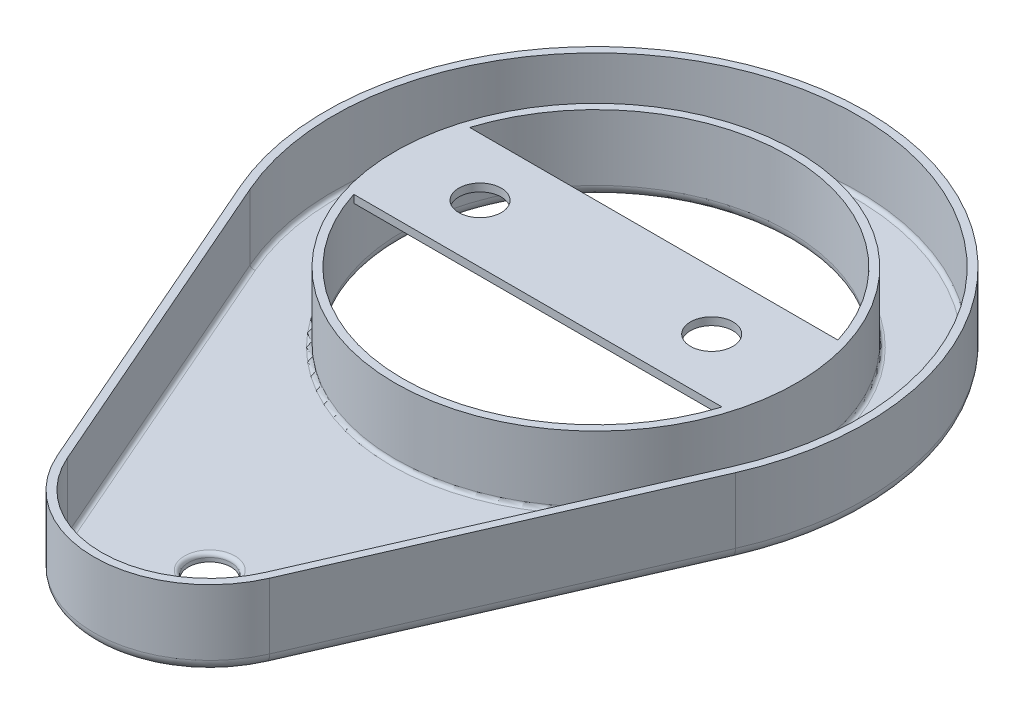
SolidWorks part; units mm, degrees
material "1.4301 (X5CrNi18-10)"
ref_plane "Front Plane" through (0, 0, 0) normal (0, 0, 1) x (1, 0, 0)
ref_plane "Top Plane" through (0, 0, 0) normal (0, 1, 0) x (1, 0, 0)
ref_plane "Right Plane" through (0, 0, 0) normal (1, 0, 0) x (0, 0, -1)
sketch "Sketch1" plane through (0, 0, 0) normal (0, 1, 0) x (1, 0, 0)
  line L0 (0, -55) -> (0, 55) construction
  line L1 (-55, 0) -> (55, 0) construction
  line L2 (13.7477, -6) -> (32.078, 36)
  line L3 (-13.7477, -6) -> (-32.078, 36)
  arc A1 (-13.7477, -6) -> (13.7477, -6) centre (0, 0) ccw
  arc A2 (32.078, 36) -> (-32.078, 36) centre (0, 50) ccw
  circle A3 centre (0, 50) radius 25
  dimension "D2" = 30
  dimension "D3" = 70
  dimension "D5" = 50
  dimension "D4" = 50
extrude "Boss-Extrude1" add sketch "Sketch1" along normal blind 10
shell "Shell1" thickness 1
sketch "Sketch3" plane through (0, 10, 0) normal (0, 1, 0) x (1, 0, 0)
  line L0 (-23.8485, 57.5) -> (23.8485, 57.5)
  line L1 (-23.8485, 42.5) -> (23.8485, 42.5)
  circle A0 centre (0, 50) radius 25 construction
  arc A1 (-23.8485, 57.5) -> (-23.8485, 42.5) centre (0, 50) ccw
  arc A2 (23.8485, 42.5) -> (23.8485, 57.5) centre (0, 50) ccw
  dimension "D1" = 15
extrude "Boss-Extrude2" add sketch "Sketch3" against normal blind 1
sketch "Sketch4" plane through (0, 1, 0) normal (0, 1, 0) x (1, 0, 0)
  circle A0 centre (0, 0) radius 2.75
  dimension "D1" = 5.5
extrude "Cut-Extrude1" cut sketch "Sketch4" against normal up to next
fillet "Fillet1" radius 0.5 6 edges at (0, 1, -24) (-21.9964, 1, -15.4) (0, 1, -84) (21.9964, 1, -15.4) (0, 1, 14) (0, 1, 2.75)
fillet "Fillet2" radius 1.5 5 edges at (0, 0, 15) (-22.9129, 0, -15) (0, 0, -85) (0, 0, -25) (22.9129, 0, -15)
sketch "Sketch5" plane through (0, 9, 0) normal (0, -1, 0) x (1, 0, 0)
  line L0 (-23.8485, -42.5) -> (23.8485, -42.5) construction
  line L1 (0, -5.5) -> (0, 5.5) construction
  circle A0 centre (15, -50) radius 2.75
  circle A1 centre (-15, -50) radius 2.75
  dimension "D2" = 5.5
  dimension "D3" = 30
  dimension "D1" = 7.5
extrude "Cut-Extrude2" cut sketch "Sketch5" against normal up to next
